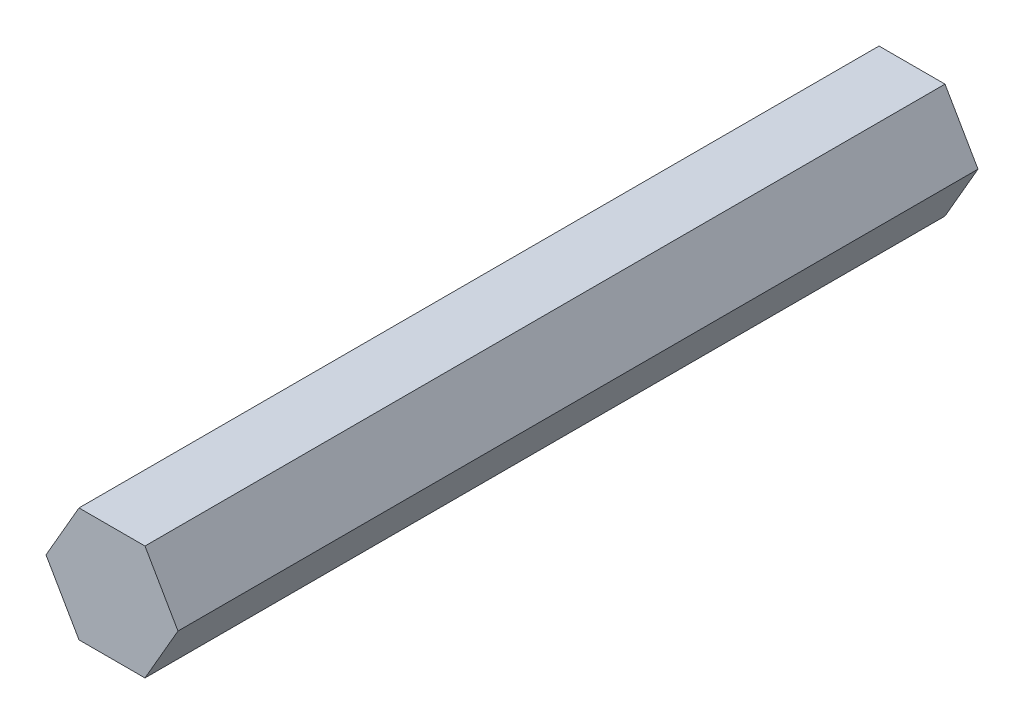
SolidWorks part; units mm, degrees
ref_plane "Front Plane" through (0, 0, 0) normal (0, 0, 1) x (1, 0, 0)
ref_plane "Top Plane" through (0, 0, 0) normal (0, 1, 0) x (1, 0, 0)
ref_plane "Right Plane" through (0, 0, 0) normal (1, 0, 0) x (0, 0, -1)
sketch "Sketch1" plane through (0, 0, 0) normal (0, 0, 1) x (1, 0, 0)
  line L1 (7.3323, 0) -> (3.6662, 6.35)
  line L2 (3.6662, 6.35) -> (-3.6662, 6.35)
  line L3 (-3.6662, 6.35) -> (-7.3323, 0)
  line L4 (-7.3323, 0) -> (-3.6662, -6.35)
  line L5 (-3.6662, -6.35) -> (3.6662, -6.35)
  line L6 (3.6662, -6.35) -> (7.3323, 0)
  circle A0 centre (0, 0) radius 6.35 construction
  dimension "D1" = 12.7
extrude "Boss-Extrude1" add sketch "Sketch1" along normal blind 88.9
